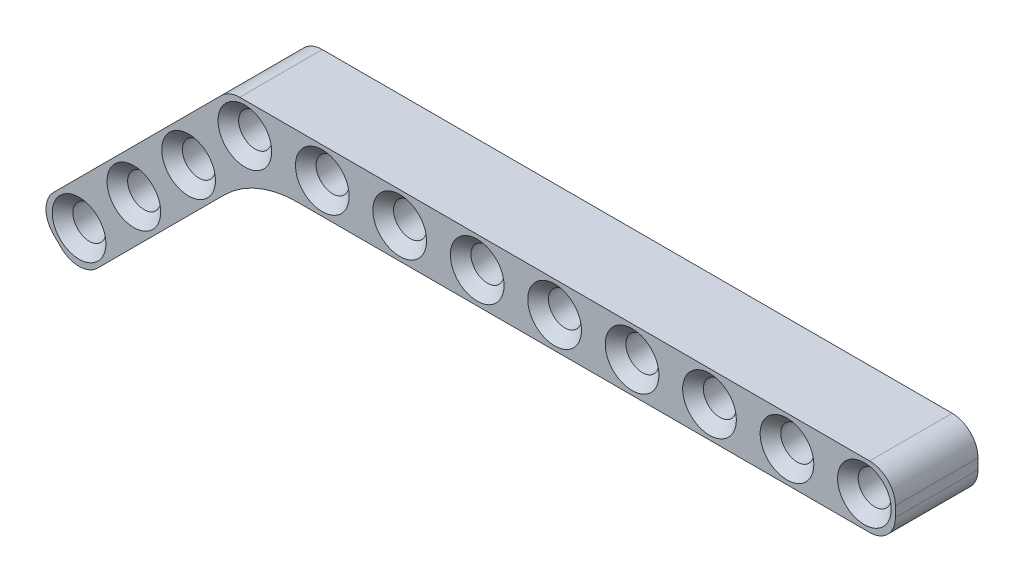
SolidWorks part; units mm, degrees
ref_plane "Front Plane" through (0, 0, 0) normal (0, 0, 1) x (1, 0, 0)
ref_plane "Top Plane" through (0, 0, 0) normal (0, 1, 0) x (1, 0, 0)
ref_plane "Right Plane" through (0, 0, 0) normal (1, 0, 0) x (0, 0, -1)
sketch "Sketch1" plane through (0, 0, 0) normal (0, 0, 1) x (1, 0, 0)
  line L1 (-0.5, 3) -> (60.5, 3)
  line L2 (-3, 0.5) -> (-3, -0.5)
  line L3 (-0.5, -3) -> (60.5, -3)
  line L4 (63, 0.5) -> (63, -0.5)
  circle A0 centre (0, 0) radius 1.6
  arc A1 (60.5, -3) -> (63, -0.5) centre (60.5, -0.5) ccw
  arc A2 (60.5, 3) -> (63, 0.5) centre (60.5, 0.5) cw
  arc A3 (-3, -0.5) -> (-0.5, -3) centre (-0.5, -0.5) ccw
  arc A4 (-0.5, 3) -> (-3, 0.5) centre (-0.5, 0.5) ccw
  circle A5 centre (7.5, 0) radius 1.6
  circle A6 centre (15, 0) radius 1.6
  circle A7 centre (22.5, 0) radius 1.6
  circle A8 centre (30, 0) radius 1.6
  circle A9 centre (37.5, 0) radius 1.6
  circle A10 centre (45, 0) radius 1.6
  circle A11 centre (52.5, 0) radius 1.6
  circle A12 centre (60, 0) radius 1.6
  point P8 (-3, 0)
  point P14 (-3, -3)
  point P17 (-3, 3)
  dimension "D1" = 3.2
  dimension "D4" = 2.5
  dimension "D2" = 6
  dimension "D3" = 3
  dimension "D6" = 7.5
  dimension "D5" = 9
extrude "Boss-Extrude1" add sketch "Sketch1" along normal blind 8
chamfer "Chamfer1" distance 1 angle 45 10 edges at (31.6, 0, 0) (31.6, 0, 8) (24.1, 0, 0) (24.1, 0, 8) (16.6, 0, 0) (16.6, 0, 8) (9.1, 0, 0) (9.1, 0, 8) (1.6, 0, 0) (1.6, 0, 8)
sketch "Sketch2" plane through (0, 0, 8) normal (0, 0, 1) x (1, 0, 0)
  line L0 (-2.2678, 2.2678) -> (-18.5292, -13.9937)
  line L1 (-18.5292, -17.5292) -> (-17.8221, -18.2363)
  line L2 (-14.2866, -18.2363) -> (0.9497, -3)
  line L4 (-0.5, -3) -> (60.5, -3) construction
  arc A0 (-0.5, 3) -> (-3, 0.5) centre (-0.5, 0.5) ccw construction
  circle A1 centre (-5.4477, -5.1548) radius 1.6
  circle A2 centre (-10.751, -10.4581) radius 1.6
  circle A3 centre (-16.0543, -15.7614) radius 1.6
  arc A4 (-18.5292, -13.9937) -> (-18.5292, -17.5292) centre (-16.7614, -15.7614) ccw
  arc A5 (-17.8221, -18.2363) -> (-14.2866, -18.2363) centre (-16.0543, -16.4685) ccw
  point P18 (-20.297, -15.7614)
  point P21 (-16.0543, -20.0041)
  arc M15 (-0.5, 3) -> (-3, 0.5) centre (-0.5, 0.5) ccw
  line M16 (-3, 0.5) -> (-3, -0.5)
  arc M17 (-3, -0.5) -> (-0.5, -3) centre (-0.5, -0.5) ccw
  line M18 (-0.5, -3) -> (60.5, -3)
  dimension "D3" = 3.2
  dimension "D8" = 2.5
  dimension "D1" = 6
  dimension "D2" = 45
  dimension "D4" = 3
  dimension "D5" = 7.5
  dimension "D7" = 3
  dimension "D6" = 3
extrude "Boss-Extrude3" add sketch "Sketch2" against normal blind 8 contours L1 A5 L2 L0 A4 A1 A2 A3 M18 M17 M16 M15
fillet "Fillet1" radius 10 1 edges at (0.9497, -3, 4)
chamfer "Chamfer2" distance 1 angle 45 6 edges at (-14.4543, -15.7614, 8) (-14.4543, -15.7614, 0) (-9.151, -10.4581, 8) (-9.151, -10.4581, 0) (-3.8477, -5.1548, 8) (-3.8477, -5.1548, 0)
chamfer "Chamfer3" distance 1 angle 45 4 edges at (46.6, 0, 0) (46.6, 0, 8) (39.1, 0, 0) (39.1, 0, 8)
chamfer "Chamfer4" distance 1 angle 45 4 edges at (61.6, 0, 0) (61.6, 0, 8) (54.1, 0, 0) (54.1, 0, 8)
